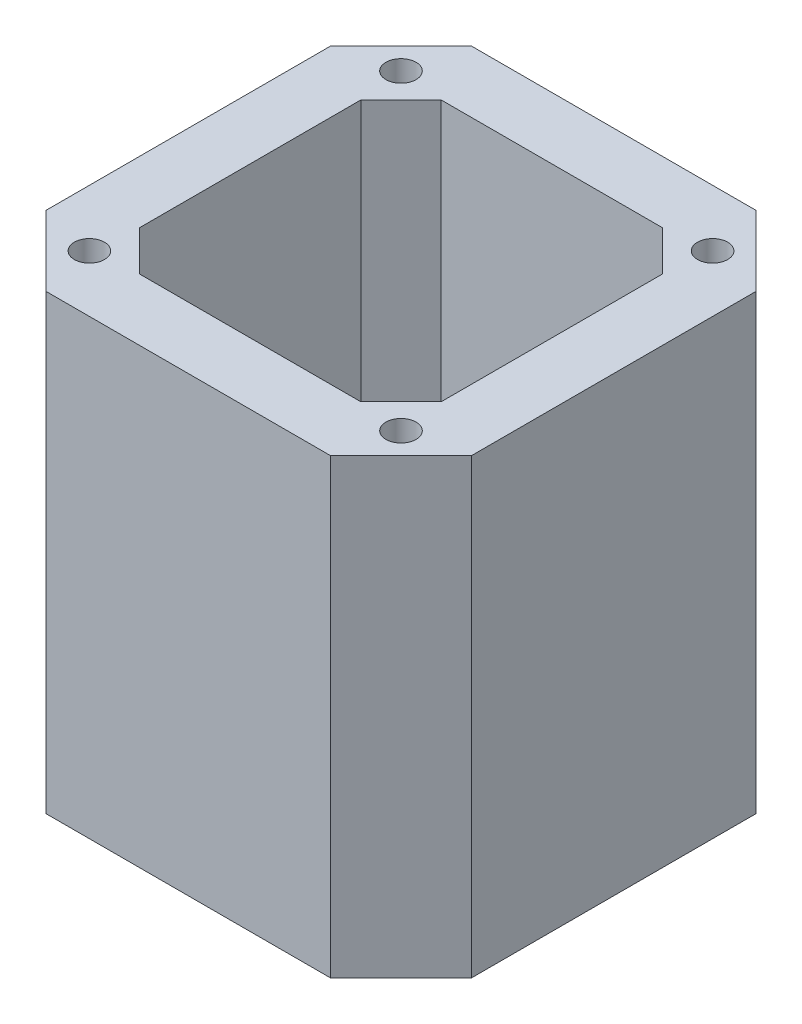
SolidWorks part; units mm, degrees
ref_plane "Front Plane" through (0, 0, 0) normal (0, 0, 1) x (1, 0, 0)
ref_plane "Top Plane" through (0, 0, 0) normal (0, 1, 0) x (1, 0, 0)
ref_plane "Right Plane" through (0, 0, 0) normal (1, 0, 0) x (0, 0, -1)
sketch "Sketch1" plane through (0, 0, 0) normal (0, 1, 0) x (1, 0, 0)
  line L0 (-21.15, 14.15) -> (-14.15, 21.15)
  line L1 (-14.15, 21.15) -> (14.15, 21.15)
  line L2 (-21.15, 14.15) -> (-21.15, -14.15)
  line L3 (-14.15, -21.15) -> (14.15, -21.15)
  line L4 (21.15, 14.15) -> (21.15, -14.15)
  line L5 (-21.15, 21.15) -> (21.15, -21.15) construction
  line L6 (-21.15, -21.15) -> (21.15, 21.15) construction
  line L7 (14.15, 21.15) -> (21.15, 14.15)
  line L8 (14.15, -21.15) -> (21.15, -14.15)
  line L9 (-21.15, -14.15) -> (-14.15, -21.15)
  point P0 (0, 0)
  dimension "D1" = 42.3
extrude "Boss-Extrude1" add sketch "Sketch1" along normal blind 45
sketch "Sketch2" plane through (0, 45, 0) normal (0, 1, 0) x (1, 0, 0)
  line L1 (-15.5, 15.5) -> (15.5, 15.5) construction
  line L2 (-15.5, 15.5) -> (-15.5, -15.5) construction
  line L3 (-15.5, -15.5) -> (15.5, -15.5) construction
  line L4 (15.5, 15.5) -> (15.5, -15.5) construction
  line L5 (-15.5, 15.5) -> (15.5, -15.5) construction
  line L6 (-15.5, -15.5) -> (15.5, 15.5) construction
  circle A0 centre (-15.5, 15.5) radius 1.5
  circle A1 centre (15.5, 15.5) radius 1.5
  circle A2 centre (-15.5, -15.5) radius 1.5
  circle A3 centre (15.5, -15.5) radius 1.5
  point P0 (0, 0)
  dimension "D2" = 3
  dimension "D1" = 31
extrude "Cut-Extrude1" cut sketch "Sketch2" against normal blind 5
sketch "Sketch3" plane through (0, 45, 0) normal (0, 1, 0) x (1, 0, 0)
  line L0 (-15, 11) -> (-11, 15)
  line L1 (-11, 15) -> (11, 15)
  line L2 (-15, 11) -> (-15, -11)
  line L3 (-11, -15) -> (11, -15)
  line L4 (15, 11) -> (15, -11)
  line L5 (-15, 15) -> (15, -15) construction
  line L6 (-15, -15) -> (15, 15) construction
  line L7 (11, 15) -> (15, 11)
  line L8 (11, -15) -> (15, -11)
  line L9 (-15, -11) -> (-11, -15)
  point P0 (0, 0)
  dimension "D1" = 30
  dimension "D2" = 30
extrude "Cut-Extrude3" cut sketch "Sketch3" against normal blind 45
